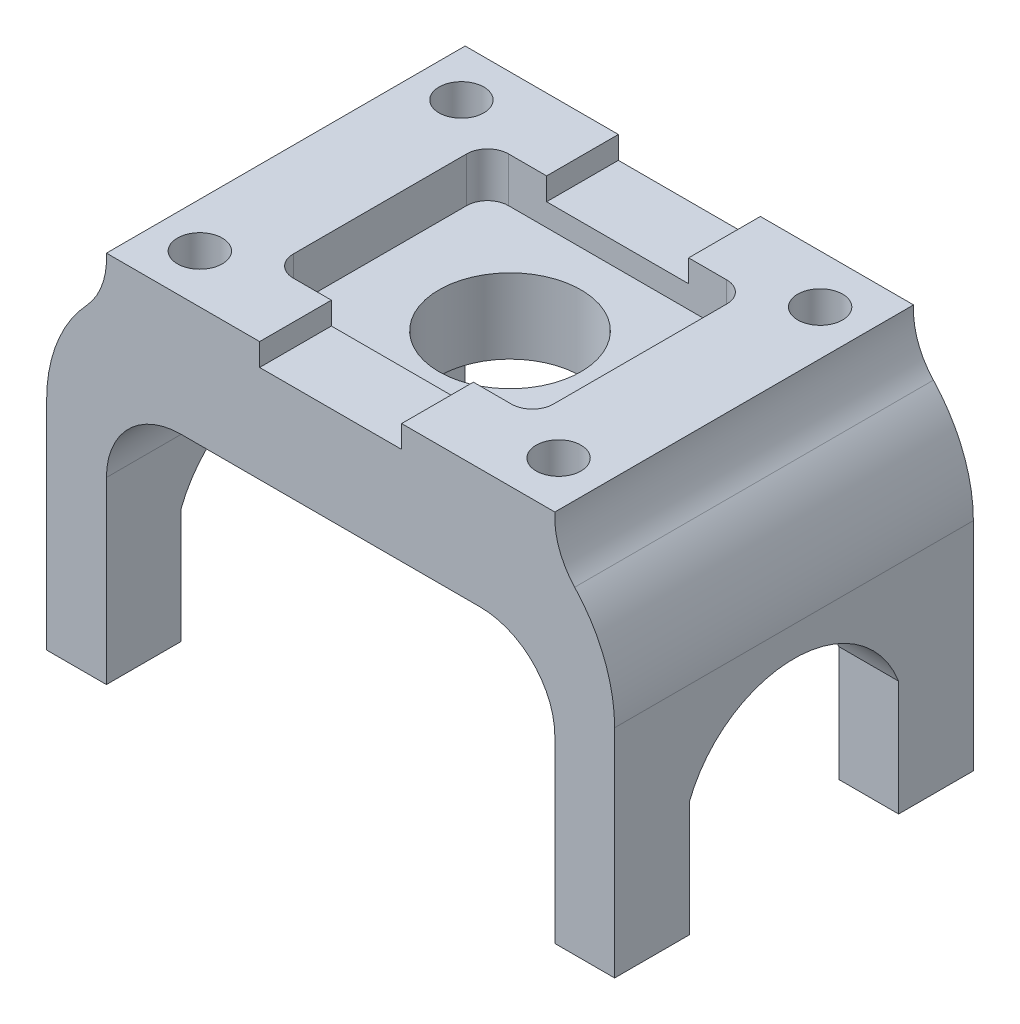
SolidWorks part; units mm, degrees
ref_plane "Frontal" through (0, 0, 0) normal (0, 0, 1) x (1, 0, 0)
ref_plane "Horizontal" through (0, 0, 0) normal (0, 1, 0) x (1, 0, 0)
ref_plane "Profile" through (0, 0, 0) normal (1, 0, 0) x (0, 0, -1)
sketch "Sketch1" plane through (0, 0, 0) normal (0, 0, 1) x (1, 0, 0)
  line L0 (1.6334, 61.2368) -> (1.6334, -73.9794) construction
  line L1 (7.7868, -20.32) -> (-23.7666, -20.32)
  line L2 (-10.4316, -3.81) -> (13.6984, -3.81)
  line L3 (13.6984, -3.81) -> (13.6984, 0)
  line L4 (13.6984, 0) -> (39.7334, 0)
  line L5 (39.7334, -33.02) -> (39.7334, -63.5)
  line L6 (39.7334, -63.5) -> (49.8934, -63.5)
  line L7 (49.8934, -63.5) -> (49.8934, -26.67)
  line L8 (-4.52, -20.32) -> (27.0334, -20.32)
  line L9 (-36.4666, -63.5) -> (-46.6266, -63.5)
  line L10 (-46.6266, -63.5) -> (-46.6266, -26.67)
  line L11 (-36.4666, -33.02) -> (-36.4666, -63.5)
  line L12 (-10.4316, -3.81) -> (-10.4316, 0)
  line L13 (-10.4316, 0) -> (-36.4666, 0)
  arc A0 (27.0334, -20.32) -> (39.7334, -33.02) centre (27.0334, -33.02) cw
  arc A1 (49.8934, -26.67) -> (43.1056, -9.3857) centre (24.4934, -26.67) ccw
  arc A2 (39.7334, 0) -> (43.1056, -9.3857) centre (52.4116, -0.7435) ccw
  arc A3 (-23.7666, -20.32) -> (-36.4666, -33.02) centre (-23.7666, -33.02) ccw
  arc A4 (-36.4666, 0) -> (-39.8387, -9.3857) centre (-49.1448, -0.7435) cw
  arc A5 (-46.6266, -26.67) -> (-39.8387, -9.3857) centre (-21.2266, -26.67) cw
  dimension "D5" = 12.7
  dimension "D1" = 12.7
  dimension "D2" = 25.4
  dimension "D9" = 20.32
  dimension "D3" = 24.13
  dimension "D4" = 26.035
  dimension "D6" = 10.16
  dimension "D7" = 36.83
  dimension "D8" = 30.48
  dimension "D10" = 3.81
extrude "Extrude1" add sketch "Sketch1" against normal blind 60.96 contours L2 L0 L1 L8 A0 L5 L6 L7 A1 A2 L4 L3 | L0 L2 L12 L13 A4 A5 L10 L9 L11 A3 L1 L8
sketch "Sketch4" plane through (0, 0, 0) normal (1, 0, 0) x (0, 0, -1)
  line L0 (12.7, -63.5) -> (12.7, -43.942)
  line L1 (60.96, -63.5) -> (0, -63.5) construction
  line L3 (48.26, -63.5) -> (48.26, -43.942)
  line L4 (0, -63.5) -> (0, -26.67) construction
  arc A0 (48.26, -43.942) -> (12.7, -43.942) centre (30.48, -50.7812) ccw
  dimension "D1" = 19.05
  dimension "D2" = 19.558
  dimension "D3" = 12.7
  dimension "D4" = 35.56
extrude "Cut-Extrude1" cut sketch "Sketch4" against normal through all and the other way through all
sketch "Sketch5" plane through (0, -3.81, 0) normal (0, 1, 0) x (-1, 0, 0)
  line L0 (-39.7334, -60.96) -> (-39.7334, 0) construction
  line L1 (-23.7314, -48.768) -> (20.4646, -48.768)
  line L2 (-23.7314, -48.768) -> (-23.7314, -12.192)
  line L3 (-23.7314, -12.192) -> (20.4646, -12.192)
  line L4 (20.4646, -48.768) -> (20.4646, -12.192)
  line L5 (10.4316, 0) -> (-13.6984, 0) construction
  dimension "D1" = 16.002
  dimension "D2" = 16.002
  dimension "D3" = 12.192
  dimension "D4" = 12.192
extrude "Cut-Extrude3" cut sketch "Sketch5" along normal blind 3.81 and the other way blind 3.81
fillet "Fillet1" radius 3.556 1 edges at (23.7314, -3.81, -12.192)
fillet "Fillet2" radius 3.556 3 edges at (23.7314, -3.81, -48.768) (-20.4646, -3.81, -12.192) (-20.4646, -3.81, -48.768)
sketch "Sketch6" plane through (0, -7.62, 0) normal (0, 1, 0) x (-1, 0, 0)
  circle A0 centre (-1.6334, -30.48) radius 12.065
  dimension "D1" = 24.13
  dimension "D2" = 18.288
  dimension "D3" = 38.1
extrude "Cut-Extrude4" cut sketch "Sketch6" against normal through all
sketch "Sketch7" plane through (0, 0, 0) normal (0, 1, 0) x (-1, 0, 0)
  line L0 (-13.6984, 0) -> (-39.7334, 0) construction
  line L1 (-39.7334, -60.96) -> (-39.7334, 0) construction
  circle A0 centre (-32.1134, -8.255) radius 3.81
  dimension "D1" = 8.255
  dimension "D2" = 7.62
extrude "Cut-Extrude5" cut sketch "Sketch7" against normal through all
sketch "Sketch8" plane through (0, 0, 0) normal (0, 1, 0) x (-1, 0, 0)
  line L0 (-32.1134, -8.255) -> (26.9864, -8.255) construction
  line L1 (-32.1134, -8.255) -> (-32.1134, -55.0569) construction
pattern_linear "LPattern1" count 2 spacing 60.96 along (-1, 0, 0) count 2 spacing 44.45 along (0, 0, -1) of "Cut-Extrude5"
